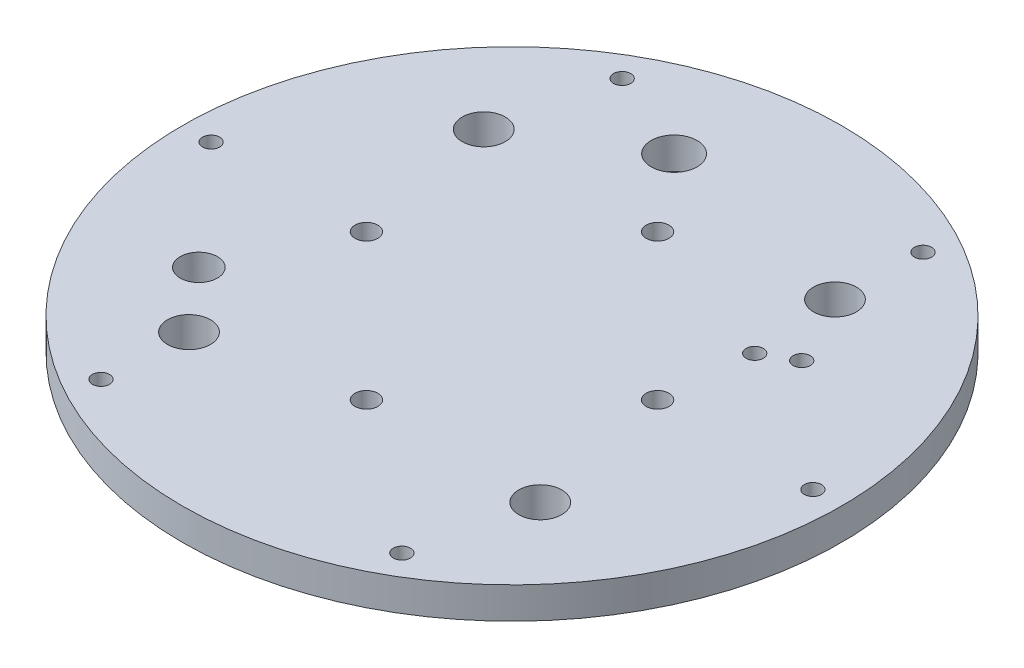
SolidWorks part; units mm, degrees
ref_plane "Front Plane" through (0, 0, 0) normal (0, 0, 1) x (1, 0, 0)
ref_plane "Top Plane" through (0, 0, 0) normal (0, 1, 0) x (1, 0, 0)
ref_plane "Right Plane" through (0, 0, 0) normal (1, 0, 0) x (0, 0, -1)
sketch "Sketch1" plane through (0, 0, 0) normal (0, 1, 0) x (1, 0, 0)
  line L0 (0, 0) -> (-52.5, 0) construction
  line L1 (0, 0) -> (-52.5, 0) construction
  circle A0 centre (0, 0) radius 57.5
  circle A1 centre (-52.5, 0) radius 1.5
  circle A2 centre (-26.25, 45.4663) radius 1.5
  circle A3 centre (26.25, 45.4663) radius 1.5
  circle A4 centre (52.5, 0) radius 1.5
  circle A5 centre (26.25, -45.4663) radius 1.5
  circle A6 centre (-26.25, -45.4663) radius 1.5
  point P17 (0, 0)
  dimension "D1" = 115
  dimension "D3" = 3
  dimension "D2" = 52.5
  dimension "D4" = 6
extrude "Boss-Extrude1" add sketch "Sketch1" along normal blind 5.5
sketch "Sketch3" plane through (0, 5.5, 0) normal (0, 1, 0) x (1, 0, 0)
  line L0 (-25.4, 0) -> (25.4, 0) construction
  line L2 (0, 25.4) -> (0, -25.4) construction
  circle A0 centre (0, 25.4) radius 2
  circle A1 centre (25.4, 0) radius 2
  circle A2 centre (0, -25.4) radius 2
  circle A3 centre (-25.4, 0) radius 2
  point P3 (0, 0)
  point P6 (0, 0)
  dimension "D2" = 4
  dimension "D1" = 50.8
extrude "Cut-Extrude1" cut sketch "Sketch3" against normal blind 5.5
sketch "Sketch4" plane through (0, 5.5, 0) normal (0, 1, 0) x (1, 0, 0)
  line L1 (0, 0) -> (-57.5, 0) construction
  line L2 (0, 0) -> (-30.6418, 25.7115) construction
  circle A0 centre (-30.6418, 25.7115) radius 3.75
  circle A1 centre (0, 0) radius 57.5 construction
  circle A2 centre (25.7115, 30.6418) radius 3.75
  circle A3 centre (30.6418, -25.7115) radius 3.75
  circle A4 centre (-25.7115, -30.6418) radius 3.75
  dimension "D2" = 7.5
  dimension "D1" = 40
  dimension "D5" = 40
  dimension "D4" = 4
extrude "Cut-Extrude3" cut sketch "Sketch4" against normal blind 5.5
sketch "Sketch5" plane through (0, 0, 0) normal (0, -1, 0) x (1, 0, 0)
  line L0 (-34.641, 20) -> (0, 0) construction
  line L1 (0, 0) -> (-30.6418, -25.7115) construction
  line L2 (0, 0) -> (-57.5, 0) construction
  circle A0 centre (-34.641, 20) radius 3.25
  circle A1 centre (0, 0) radius 57.5 construction
  dimension "D2" = 6.5
  dimension "D1" = 30
extrude "Cut-Extrude4" cut sketch "Sketch5" against normal blind 10
sketch "Sketch6" plane through (0, 0, 0) normal (0, -1, 0) x (1, 0, 0)
  line L0 (-10.3528, -38.637) -> (0, 0) construction
  line L1 (0, 0) -> (-57.5, 0) construction
  line L2 (32.0429, -18.5) -> (0, 0) construction
  circle A0 centre (-10.3528, -38.637) radius 4
  circle A1 centre (0, 0) radius 57.5 construction
  circle A2 centre (32.0429, -18.5) radius 1.5
  circle A3 centre (26.8468, -15.5) radius 1.5
  dimension "D1" = 8
  dimension "D4" = 3
  dimension "D2" = 40
  dimension "D3" = 75
  dimension "D5" = 37
  dimension "D6" = 75
  dimension "D7" = 6
extrude "Cut-Extrude5" cut sketch "Sketch6" against normal blind 10
